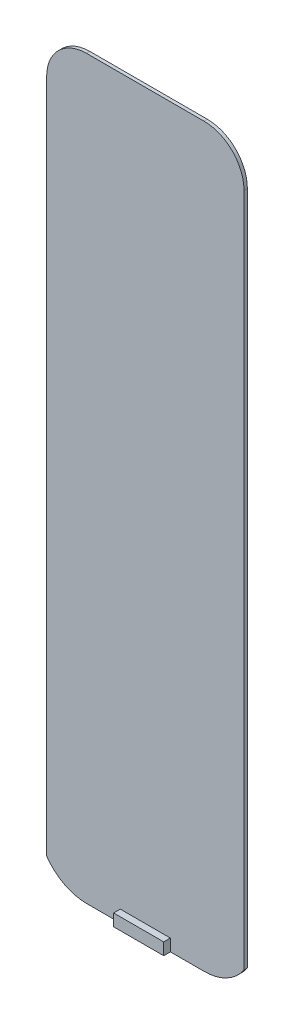
SolidWorks part; units mm, degrees
ref_plane "前基準面" through (0, 0, 0) normal (0, 0, 1) x (1, 0, 0)
ref_plane "上基準面" through (0, 0, 0) normal (0, 1, 0) x (1, 0, 0)
ref_plane "右基準面" through (0, 0, 0) normal (1, 0, 0) x (0, 0, -1)
sketch "草圖1" plane through (0, 0, 0) normal (0, 0, 1) x (1, 0, 0)
  line L0 (-17.5244, -119.1015) -> (-17.5244, -88.4068) construction
  line L1 (-17.6, 110.46) -> (17.6, 110.46)
  line L4 (29.56, 98.5) -> (29.56, -103.7646)
  line L5 (17.6756, -110.1) -> (-17.5244, -110.1)
  line L6 (0, 380.0661) -> (0, -159.1461) construction
  line L9 (0, -99.7501) -> (0, -120.4499) construction
  line L10 (-29.56, 98.5) -> (-29.56, -103.7646)
  arc A1 (17.6, 110.46) -> (29.56, 98.5) centre (17.6, 98.5) cw
  arc A5 (-17.6, 110.46) -> (-29.56, 98.5) centre (-17.6, 98.5) ccw
  arc A6 (-17.5244, -110.1) -> (-29.56, -103.7646) centre (-17.5244, -95.5) cw
  arc A8 (29.56, -103.7646) -> (17.6756, -110.1) centre (17.6756, -95.7856) cw
  point P0 (0, 0)
  point P13 (0, -110.1)
  point P25 (0, 110.46)
  dimension "D3" = 11.96
  dimension "D4" = 14.6
  dimension "D2" = 220.56
  dimension "D1" = 35.2
  dimension "D5" = 35.2
extrude "填料-伸長1" add sketch "草圖1" along normal mid plane 1
sketch "草圖2" plane through (0, -110.1, 0) normal (0, -1, 0) x (1, 0, 0)
  line L0 (0, 7.5697) -> (0, -7.0587) construction
  line L2 (-7.5, -2.5) -> (7.5, -2.5)
  line L3 (-7.5, -2.5) -> (-7.5, -0.5)
  line L4 (-7.5, 2.5) -> (7.5, 2.5)
  line L5 (7.5, -2.5) -> (7.5, -0.5)
  line L6 (-7.5, -2.5) -> (7.5, 2.5) construction
  line L7 (-7.5, 2.5) -> (7.5, -2.5) construction
  line L11 (-7.5, 0.5) -> (7.5, 0.5)
  line L12 (-17.5244, 0.5) -> (17.6756, 0.5) construction
  line L13 (7.5, -0.5) -> (-7.5, -0.5)
  line L14 (-17.5244, -0.5) -> (17.6756, -0.5) construction
  line L15 (-7.5, 0.5) -> (-7.5, 2.5)
  line L16 (7.5, 0.5) -> (7.5, 2.5)
  point P3 (0, 0)
  dimension "D1" = 2
  dimension "D2" = 15
extrude "填料-伸長2" add sketch "草圖2" against normal blind 3.6
